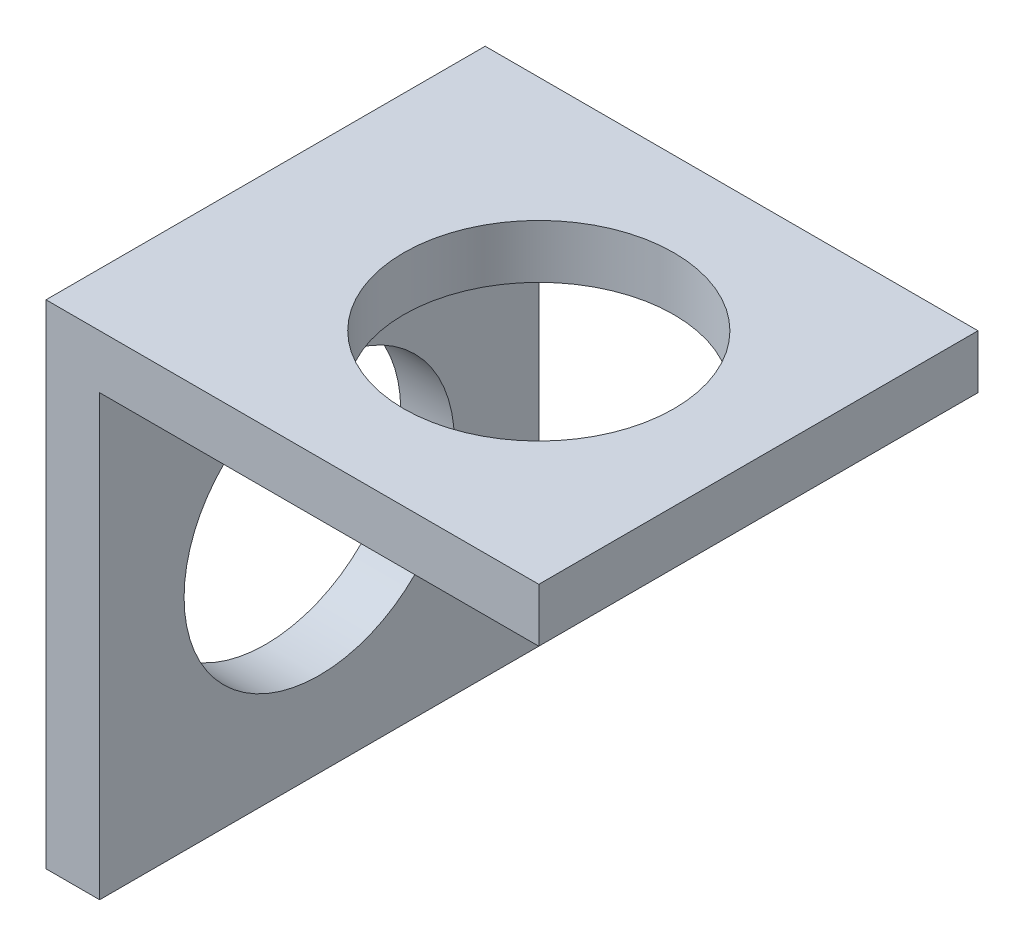
SolidWorks part; units mm, degrees
ref_plane "Front Plane" through (0, 0, 0) normal (0, 0, 1) x (1, 0, 0)
ref_plane "Top Plane" through (0, 0, 0) normal (0, 1, 0) x (1, 0, 0)
ref_plane "Right Plane" through (0, 0, 0) normal (1, 0, 0) x (0, 0, -1)
sketch "Sketch1" plane through (0, 0, 0) normal (0, 0, 1) x (1, 0, 0)
  line L1 (0, 0) -> (6.35, 0)
  line L2 (0, 0) -> (0, 32.9731)
  line L4 (6.35, 0) -> (6.35, 52)
  line L5 (6.35, 52) -> (58.35, 52)
  line L6 (0, 32.9731) -> (0, 58.35)
  line L7 (0, 58.35) -> (58.35, 58.35)
  line L8 (58.35, 52) -> (58.35, 58.35)
  dimension "D1" = 6.35
  dimension "D2" = 6.35
  dimension "D3" = 52
  dimension "D4" = 52
extrude "Boss-Extrude1" add sketch "Sketch1" along normal blind 52
sketch "Sketch2" plane through (0, 52, 0) normal (0, -1, 0) x (-1, 0, 0)
  line L0 (-6.35, -52) -> (-58.35, 0) construction
  line L1 (-58.35, 0) -> (-58.35, -52) construction
  line L2 (-58.35, -52) -> (-6.35, 0) construction
  circle A0 centre (-32.35, -26) radius 16
extrude "Cut-Extrude1" cut sketch "Sketch2" against normal blind 52
sketch "Sketch3" plane through (6.35, 0, 0) normal (1, 0, 0) x (0, 0, -1)
  line L0 (-52, 52) -> (0, 0) construction
  line L1 (0, 0) -> (0, 52) construction
  line L2 (0, 52) -> (-52, 0) construction
  circle A0 centre (-26, 26) radius 16
extrude "Cut-Extrude2" cut sketch "Sketch3" against normal blind 52
